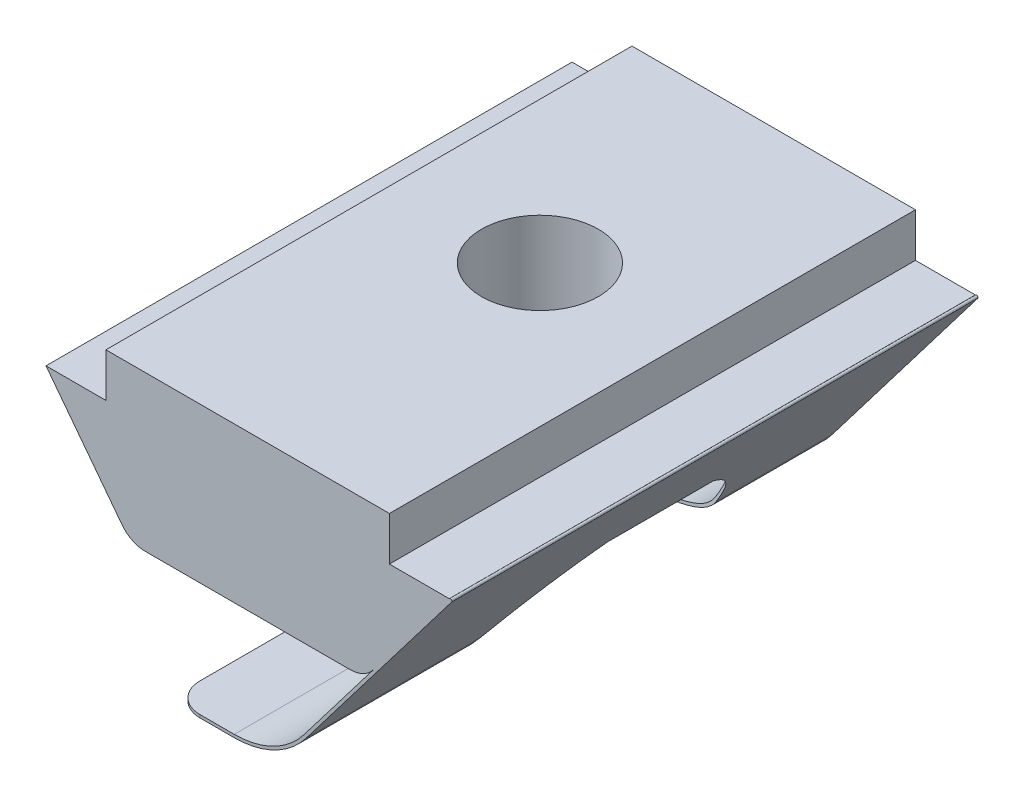
SolidWorks part; units mm, degrees
material "Оцинкованная сталь"
ref_plane "Спереди" through (0, 0, 0) normal (0, 0, 1) x (1, 0, 0)
ref_plane "Сверху" through (0, 0, 0) normal (0, 1, 0) x (1, 0, 0)
ref_plane "Справа" through (0, 0, 0) normal (1, 0, 0) x (0, 0, -1)
sketch "Эскиз1" plane through (0, 0, 0) normal (0, 0, 1) x (1, 0, 0)
  line L0 (0, 0) -> (0, 114.7697) construction
  line L1 (3.5052, 0) -> (-3.5052, 0)
  line L2 (-4.3002, 0.3933) -> (-6.9, 3.8)
  line L3 (-6.9, 3.8) -> (-4.85, 3.8)
  line L4 (-4.85, 3.8) -> (-4.85, 5.3)
  line L5 (-4.85, 5.3) -> (4.85, 5.3)
  line L6 (4.85, 3.8) -> (4.85, 5.3)
  line L7 (6.9, 3.8) -> (4.85, 3.8)
  line L8 (4.3002, 0.3933) -> (6.9, 3.8)
  arc A0 (-3.5052, 0) -> (-4.3002, 0.3933) centre (-3.5052, 1) cw
  arc A1 (3.5052, 0) -> (4.3002, 0.3933) centre (3.5052, 1) ccw
  point P11 (-4, 0)
  point P16 (0, 5.3)
  point P18 (4, 0)
  dimension "D6" = 1
  dimension "D1" = 4.85
  dimension "D2" = 1.5
  dimension "D3" = 6.9
  dimension "D4" = 5.3
  dimension "D5" = 4
extrude "Бобышка-Вытянуть1" add sketch "Эскиз1" along normal blind 10 and the other way blind 8
sketch "Эскиз2" plane through (0, 5.3, 0) normal (0, 1, 0) x (1, 0, 0)
  circle A0 centre (0, 0) radius 2
  dimension "D1" = 4
extrude "Вырез-Вытянуть1" cut sketch "Эскиз2" against normal through all
sketch "Эскиз3" plane through (0, 0, 10) normal (0, 0, 1) x (1, 0, 0)
  line L0 (6.9, 3.8) -> (1.9242, -2.72)
  line L1 (-0.4607, -3.9) -> (-2.6304, -3.9)
  line L2 (4.3002, 0.3933) -> (6.9, 3.8) construction
  line L3 (4.85, 5.3) -> (-4.85, 5.3) construction
  line L4 (6.9795, 3.7393) -> (2.0037, -2.7807)
  line L5 (-0.4607, -4) -> (-2.6304, -4)
  arc A0 (-0.4607, -3.9) -> (1.9242, -2.72) centre (-0.4607, -0.9) ccw
  arc A1 (-0.4607, -4) -> (2.0037, -2.7807) centre (-0.4607, -0.9) ccw
  arc A2 (6.9, 3.8) -> (6.9795, 3.7393) centre (6.9397, 3.7697) cw
  arc A3 (-2.6304, -3.9) -> (-2.6304, -4) centre (-2.6304, -3.95) ccw
  dimension "D2" = 3
  dimension "D1" = 9.2
  dimension "D3" = 0.1
extrude "Бобышка-Вытянуть2" add sketch "Эскиз3" against normal up to surface (18 mm away) up to face at (0, 2.6401, -8)
sketch "Эскиз4" plane through (0, -4, 0) normal (0, -1, 0) x (1, 0, 0)
  line L0 (0, 4.5) -> (-4.5, 4.5)
  line L1 (-4.5, 4.5) -> (-4.5, 0)
  line L2 (-4.5, 0) -> (-4.5, -4.5)
  line L3 (-4.5, -4.5) -> (0, -4.5)
  arc A0 (0, -4.5) -> (0, 4.5) centre (0, 0) ccw
  dimension "D1" = 9
extrude "Вырез-Вытянуть2" cut sketch "Эскиз4" against normal up to surface (4 mm away) up to face at (0, 0, 2)
sketch "Эскиз5" plane through (0, -4, 0) normal (0, -1, 0) x (1, 0, 0)
  line L1 (-2.6304, 10) -> (-2.6804, 10)
  line L2 (-2.6304, 10) -> (-2.6304, -8)
  line L3 (-2.6304, -8) -> (-2.6804, -8)
  line L4 (-2.6804, 10) -> (-2.6804, -8)
extrude "Вырез-Вытянуть3" cut sketch "Эскиз5" against normal blind 1
fillet "Скругление1" radius 1 4 edges at (-2.6304, -3.95, -4.5) (-2.6304, -3.95, -8) (-2.6304, -3.95, 4.5) (-2.6304, -3.95, 10)
